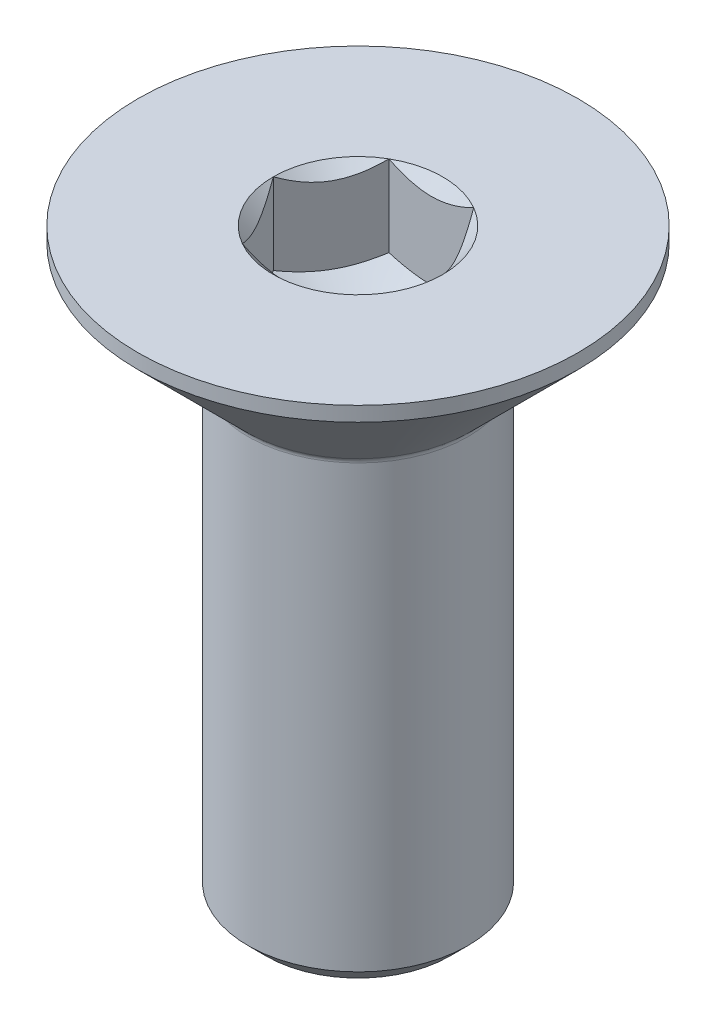
SolidWorks part; units mm, degrees
ref_plane "Plano frontal" through (0, 0, 0) normal (0, 0, 1) x (1, 0, 0)
ref_plane "Plano superior" through (0, 0, 0) normal (0, 1, 0) x (1, 0, 0)
ref_plane "Plano direito" through (0, 0, 0) normal (1, 0, 0) x (0, 0, -1)
sketch "Esboço1" plane through (0, 0, 0) normal (0, 0, 1) x (1, 0, 0)
  line L0 (0, -1000) -> (0, 49000) construction
  line L1 (0, -1.8009) -> (1, -1.2)
  line L2 (1, -1.2) -> (1, 0)
  line L3 (1, 0) -> (3, 0)
  line L4 (3, 0) -> (3, -0.2)
  line L5 (3, -0.2) -> (1.5293, -1.6707)
  line L6 (1.5, -1.7414) -> (1.5, -7.75)
  line L7 (1.5, -7.75) -> (1.25, -8)
  line L8 (1.25, -8) -> (0, -8)
  line L9 (0, -8) -> (0, -1.8009)
  arc A0 (1.5293, -1.6707) -> (1.5, -1.7414) centre (1.6, -1.7414) ccw
  dimension "RAIO_CABECA" = 0.1
  dimension "DIAMETRO_SEXTAVADO" = 2
  dimension "D2" = 59
  dimension "DIAMETRO_CABECA" = 6
  dimension "ALTURA_FACE" = 0.2
  dimension "ANGULO_PONTA" = 45
  dimension "CHANFRO_PONTA" = 0.25
  dimension "DIAMETRO_CORPO" = 3
  dimension "PROFUNDIDADE_SEXTAVADO" = 1.2
  dimension "COMPRIMENTO" = 8
revolve "Revolução1" add sketch "Esboço1" angle 360 about L0
sketch "Esboço2" plane through (0, 0, 0) normal (0, 1, 0) x (1, 0, 0)
  line L1 (-1.1547, 0) -> (-0.5774, -1)
  line L2 (-0.5774, -1) -> (0.5774, -1)
  line L3 (0.5774, -1) -> (1.1547, 0)
  line L4 (1.1547, 0) -> (0.5774, 1)
  line L5 (0.5774, 1) -> (-0.5774, 1)
  line L6 (-0.5774, 1) -> (-1.1547, 0)
  circle A0 centre (0, 0) radius 1 construction
  circle A1 centre (0, 0) radius 1 construction
extrude "Corte-extrusão1" cut sketch "Esboço2" against normal up to surface (1.107 mm away)
sketch "Esboço3" plane through (0, 0, 0) normal (0, 0, 1) x (1, 0, 0)
  line L0 (0, -1000) -> (0, 49000) construction
  line L1 (1.1547, 0) -> (0, -1.1547)
  line L2 (0, -1.1547) -> (0, 0)
  line L3 (0, 0) -> (1.1547, 0)
  dimension "D1" = 45
revolve "Corte-Revolução1" cut sketch "Esboço3" angle 360 about L0
sketch "Esboço4" plane through (0, 0, 0) normal (0, 0, 1) x (1, 0, 0)
  line L0 (-1.5, -7) -> (1.5, -7)
  line L1 (-1.5, -1.7414) -> (-1.5, -7.75) construction
  line L2 (1.5, -7.75) -> (1.5, -1.7414) construction
  line L3 (-1.25, -8) -> (1.25, -8) construction
  dimension "COMPRIMENTO_ROSCA" = 1
split line "Linha de divisão2" [suppressed]
